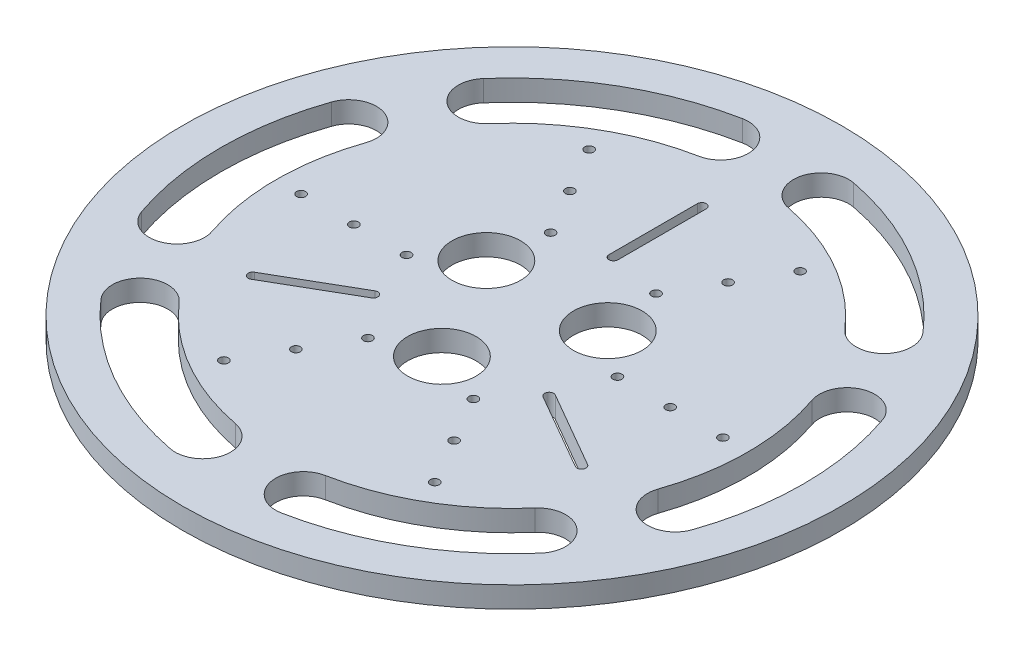
SolidWorks part; units mm, degrees
ref_plane "Front Plane" through (0, 0, 0) normal (0, 0, 1) x (1, 0, 0)
ref_plane "Top Plane" through (0, 0, 0) normal (0, 1, 0) x (1, 0, 0)
ref_plane "Right Plane" through (0, 0, 0) normal (1, 0, 0) x (0, 0, -1)
sketch "Sketch1" plane through (0, 0, 0) normal (0, 1, 0) x (1, 0, 0)
  line L0 (100, 0) -> (-100, 0)
  circle A0 centre (0, 0) radius 100
  dimension "D1" = 200
extrude "Boss-Extrude4" add sketch "Sketch1" along normal blind 8 from offset 175 separate body contours A0
sketch "Sketch15" plane through (0, 183, 0) normal (0, 1, 0) x (1, 0, 0)
  line L0 (0, 43.5) -> (0, 38.5) construction
  line L1 (0, 57) -> (0, 72) construction
  line L2 (1.7, 38.5) -> (1.7, 72)
  line L3 (-1.7, 72) -> (-1.7, 38.5)
  line L4 (32.492, -20.7222) -> (61.5038, -37.4722)
  line L5 (63.2038, -34.5278) -> (34.192, -17.7778)
  line L6 (37.6721, -21.75) -> (33.342, -19.25) construction
  line L7 (49.3634, -28.5) -> (62.3538, -36) construction
  line L8 (-34.192, -17.7778) -> (-63.2038, -34.5278)
  line L9 (-61.5038, -37.4722) -> (-32.492, -20.7222)
  line L10 (-37.6721, -21.75) -> (-33.342, -19.25) construction
  line L11 (-49.3634, -28.5) -> (-62.3538, -36) construction
  arc A0 (1.7, 72) -> (-1.7, 72) centre (0, 72) ccw
  arc A1 (-1.7, 38.5) -> (1.7, 38.5) centre (0, 38.5) ccw
  arc A2 (61.5038, -37.4722) -> (63.2038, -34.5278) centre (62.3538, -36) ccw
  arc A3 (34.192, -17.7778) -> (32.492, -20.7222) centre (33.342, -19.25) ccw
  arc A4 (-63.2038, -34.5278) -> (-61.5038, -37.4722) centre (-62.3538, -36) ccw
  arc A5 (-32.492, -20.7222) -> (-34.192, -17.7778) centre (-33.342, -19.25) ccw
  point P7 (0, 0)
  point P8 (0, 0)
  point P13 (0, 0)
  point P30 (0, 0)
  dimension "D1" = 3
  dimension "D2" = 1.7
  dimension "D3" = 33.5
  dimension "D5" = 38.5
extrude "Cut-Extrude5" cut sketch "Sketch15" against normal blind 10
sketch "Sketch19" plane through (0, 183, 0) normal (0, 1, 0) x (1, 0, 0)
  circle A0 centre (0, 0) radius 100
  circle A1 centre (0, 0) radius 125
extrude "Boss-Extrude11" add sketch "Sketch19" against normal blind 8
sketch "Sketch20" plane through (0, 183, 0) normal (0, 1, 0) x (1, 0, 0)
  line L0 (30, -51.9615) -> (20, -34.641) construction
  line L1 (30, -51.9615) -> (40, -69.282) construction
  line L2 (-30, -51.9615) -> (-20, -34.641) construction
  line L3 (-30, -51.9615) -> (-40, -69.282) construction
  line L4 (-60, 0) -> (-40, 0) construction
  line L5 (-60, 0) -> (-80, 0) construction
  line L6 (-30, 51.9615) -> (-20, 34.641) construction
  line L7 (-30, 51.9615) -> (-40, 69.282) construction
  line L8 (30, 51.9615) -> (20, 34.641) construction
  line L9 (30, 51.9615) -> (40, 69.282) construction
  line L10 (60, 0) -> (40, 0) construction
  line L11 (60, 0) -> (80, 0) construction
  circle A0 centre (30, -51.9615) radius 1.7
  circle A1 centre (40, -69.282) radius 1.7
  circle A2 centre (20, -34.641) radius 1.7
  circle A3 centre (-30, -51.9615) radius 1.7
  circle A4 centre (-40, -69.282) radius 1.7
  circle A5 centre (-20, -34.641) radius 1.7
  circle A6 centre (-60, 0) radius 1.7
  circle A7 centre (-80, 0) radius 1.7
  circle A8 centre (-40, 0) radius 1.7
  circle A9 centre (-30, 51.9615) radius 1.7
  circle A10 centre (-40, 69.282) radius 1.7
  circle A11 centre (-20, 34.641) radius 1.7
  circle A12 centre (30, 51.9615) radius 1.7
  circle A13 centre (40, 69.282) radius 1.7
  circle A14 centre (20, 34.641) radius 1.7
  circle A15 centre (60, 0) radius 1.7
  circle A16 centre (80, 0) radius 1.7
  circle A17 centre (40, 0) radius 1.7
  arc A18 (-75.457, 65.6219) -> (-19.032, 98.1722) centre (0, 0) cw construction
  arc A19 (-21.0321, 108.489) -> (-83.3867, 72.518) centre (0, 0) ccw
  arc A20 (-17.032, 87.8554) -> (-67.5273, 58.7258) centre (0, 0) ccw
  arc A21 (-17.032, 87.8554) -> (-21.0321, 108.489) centre (-19.032, 98.1722) ccw
  arc A22 (-83.3867, 72.518) -> (-67.5273, 58.7258) centre (-75.457, 65.6219) ccw
  arc A23 (19.1017, 98.1587) -> (75.5036, 65.5683) centre (0, 0) cw construction
  arc A24 (83.4382, 72.4588) -> (21.1091, 108.474) centre (0, 0) ccw
  arc A25 (67.569, 58.6778) -> (17.0943, 87.8433) centre (0, 0) ccw
  arc A26 (67.569, 58.6778) -> (83.4382, 72.4588) centre (75.5036, 65.5683) ccw
  arc A27 (21.1091, 108.474) -> (17.0943, 87.8433) centre (19.1017, 98.1587) ccw
  arc A28 (94.5588, 32.5368) -> (94.5356, -32.6039) centre (0, 0) cw construction
  arc A29 (104.4703, -36.0302) -> (104.4958, 35.956) centre (0, 0) ccw
  arc A30 (84.601, -29.1776) -> (84.6217, 29.1175) centre (0, 0) ccw
  arc A31 (84.601, -29.1776) -> (104.4703, -36.0302) centre (94.5356, -32.6039) ccw
  arc A32 (104.4958, 35.956) -> (84.6217, 29.1175) centre (94.5588, 32.5368) ccw
  arc A33 (75.457, -65.6219) -> (19.032, -98.1722) centre (0, 0) cw construction
  arc A34 (21.0321, -108.489) -> (83.3867, -72.518) centre (0, 0) ccw
  arc A35 (17.032, -87.8554) -> (67.5273, -58.7258) centre (0, 0) ccw
  arc A36 (17.032, -87.8554) -> (21.0321, -108.489) centre (19.032, -98.1722) ccw
  arc A37 (83.3867, -72.518) -> (67.5273, -58.7258) centre (75.457, -65.6219) ccw
  arc A38 (-19.1017, -98.1587) -> (-75.5036, -65.5683) centre (0, 0) cw construction
  arc A39 (-83.4382, -72.4588) -> (-21.1091, -108.474) centre (0, 0) ccw
  arc A40 (-67.569, -58.6778) -> (-17.0943, -87.8433) centre (0, 0) ccw
  arc A41 (-67.569, -58.6778) -> (-83.4382, -72.4588) centre (-75.5036, -65.5683) ccw
  arc A42 (-21.1091, -108.474) -> (-17.0943, -87.8433) centre (-19.1017, -98.1587) ccw
  arc A43 (-94.5588, -32.5368) -> (-94.5356, 32.6039) centre (0, 0) cw construction
  arc A44 (-104.4703, 36.0302) -> (-104.4958, -35.956) centre (0, 0) ccw
  arc A45 (-84.601, 29.1776) -> (-84.6217, -29.1175) centre (0, 0) ccw
  arc A46 (-84.601, 29.1776) -> (-104.4703, 36.0302) centre (-94.5356, 32.6039) ccw
  arc A47 (-104.4958, -35.956) -> (-84.6217, -29.1175) centre (-94.5588, -32.5368) ccw
  point P39 (0, 0)
  point P41 (-49.9693, 86.6203)
  point P51 (50.0307, 86.5848)
  point P58 (100, -0.0355)
  point P65 (49.9693, -86.6203)
  point P72 (-50.0307, -86.5848)
  point P79 (-100, 0.0355)
  point P84 (0, 0)
  dimension "D1" = 6
extrude "Cut-Extrude8" cut sketch "Sketch20" against normal up to surface (8 mm away) up to face at (0, 175, -55.25)
sketch "Sketch22" plane through (0, 0, 0) normal (0, 1, 0) x (1, 0, 0)
  circle A0 centre (23.0347, 13.2991) radius 13
  circle A1 centre (0, -26.5981) radius 13
  circle A2 centre (-23.0347, 13.2991) radius 13
extrude "Cut-Extrude9" cut sketch "Sketch22" against normal up to surface (8 mm away) from surface at 183 up to face at (60, 175, 1.7) starting at face at (60, 183, 1.7)
equation "\"R\"= 100"
equation "\"D1@Sketch1\"=2*\"R\""
equation "\"contact_angle\"= 52deg"
equation "\"wheel_D\"= 60"
equation "\"D1@Sketch5\"=\"wheel_D\""
equation "\"motor_D\"= 25"
equation "\"motor_towheel_L\"=55"
equation "\"D2@Sketch5\"=\"motor_D\""
equation "\"D1@Boss-Extrude2\"=\"motor_towheel_L\""
equation "\"D19@Boss-Extrude4\"=1.75*\"R\""
